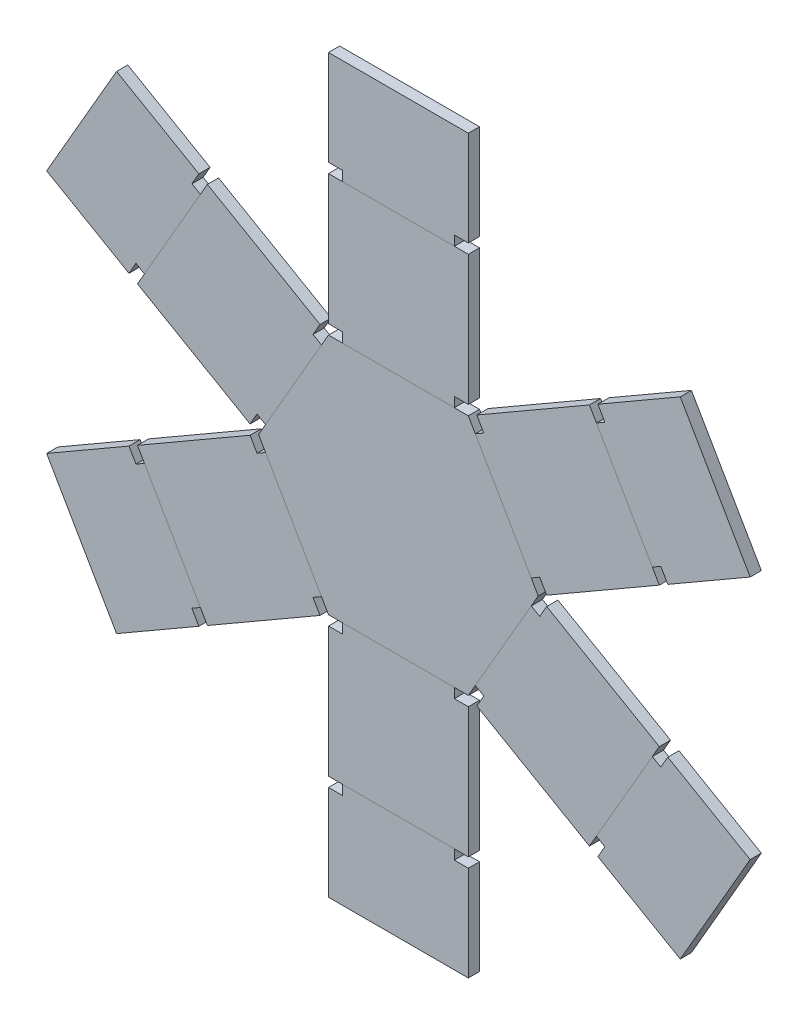
SolidWorks part; units mm, degrees
ref_plane "Front" through (0, 0, 0) normal (0, 0, 1) x (1, 0, 0)
ref_plane "Top" through (0, 0, 0) normal (0, 1, 0) x (1, 0, 0)
ref_plane "Right" through (0, 0, 0) normal (1, 0, 0) x (0, 0, -1)
sketch "Sketch1" plane through (0, 0, 0) normal (0, 0, 1) x (1, 0, 0)
  line L1 (-1, 0) -> (-0.5, -0.866)
  line L2 (-0.5, -0.866) -> (0.5, -0.866)
  line L3 (0.5, -0.866) -> (1, 0)
  line L4 (1, 0) -> (0.5, 0.866)
  line L5 (0.5, 0.866) -> (-0.5, 0.866)
  line L6 (-0.5, 0.866) -> (-1, 0)
  circle A0 centre (0, 0) radius 0.866 construction
  dimension "D1" = 2
extrude "Boss-Extrude1" add sketch "Sketch1" along normal blind 0.08
sketch "Sketch2" plane through (0, 0, 0.08) normal (0, 0, 1) x (1, 0, 0)
  line L0 (-0.95, 0.0866) -> (-0.55, 0.7794)
  line L1 (-1.0606, 0.035) -> (-1.866, 0.5)
  line L2 (-0.5606, 0.901) -> (-1.366, 1.366)
  line L3 (-1.866, 0.5) -> (-1.366, 1.366)
  line L26 (-0.95, 0.0866) -> (-1.0106, 0.1216)
  line L27 (-1.0606, 0.035) -> (-1.0106, 0.1216)
  line L30 (-0.55, 0.7794) -> (-0.6106, 0.8144)
  line L31 (-0.5606, 0.901) -> (-0.6106, 0.8144)
  line L32 (-0.5, 0.866) -> (-1, 0) construction
  line L33 (-1, 0) -> (-1.0606, 0.035) construction
  line L34 (-0.5, 0.866) -> (-0.5606, 0.901) construction
  line L35 (-0.4, 0.866) -> (0.4, 0.866)
  line L36 (0.4, 0.866) -> (0.4, 0.936)
  line L37 (0.5, 0.936) -> (0.4, 0.936)
  line L38 (0.5, 0.936) -> (0.5, 1.866)
  line L39 (-0.5, 1.866) -> (0.5, 1.866)
  line L40 (-0.5, 0.936) -> (-0.5, 1.866)
  line L41 (-0.5, 0.936) -> (-0.4, 0.936)
  line L42 (-0.4, 0.866) -> (-0.4, 0.936)
  line L43 (0.55, 0.7794) -> (0.95, 0.0866)
  line L44 (0.95, 0.0866) -> (1.0106, 0.1216)
  line L45 (1.0606, 0.035) -> (1.0106, 0.1216)
  line L46 (1.0606, 0.035) -> (1.866, 0.5)
  line L47 (1.366, 1.366) -> (1.866, 0.5)
  line L48 (0.5606, 0.901) -> (1.366, 1.366)
  line L49 (0.5606, 0.901) -> (0.6106, 0.8144)
  line L50 (0.55, 0.7794) -> (0.6106, 0.8144)
  line L51 (0.95, -0.0866) -> (0.55, -0.7794)
  line L52 (0.55, -0.7794) -> (0.6106, -0.8144)
  line L53 (0.5606, -0.901) -> (0.6106, -0.8144)
  line L54 (0.5606, -0.901) -> (1.366, -1.366)
  line L55 (1.866, -0.5) -> (1.366, -1.366)
  line L56 (1.0606, -0.035) -> (1.866, -0.5)
  line L57 (1.0606, -0.035) -> (1.0106, -0.1216)
  line L58 (0.95, -0.0866) -> (1.0106, -0.1216)
  line L59 (0.4, -0.866) -> (-0.4, -0.866)
  line L60 (-0.4, -0.866) -> (-0.4, -0.936)
  line L61 (-0.5, -0.936) -> (-0.4, -0.936)
  line L62 (-0.5, -0.936) -> (-0.5, -1.866)
  line L63 (0.5, -1.866) -> (-0.5, -1.866)
  line L64 (0.5, -0.936) -> (0.5, -1.866)
  line L65 (0.5, -0.936) -> (0.4, -0.936)
  line L66 (0.4, -0.866) -> (0.4, -0.936)
  line L67 (-0.55, -0.7794) -> (-0.95, -0.0866)
  line L68 (-0.95, -0.0866) -> (-1.0106, -0.1216)
  line L69 (-1.0606, -0.035) -> (-1.0106, -0.1216)
  line L70 (-1.0606, -0.035) -> (-1.866, -0.5)
  line L71 (-1.366, -1.366) -> (-1.866, -0.5)
  line L72 (-0.5606, -0.901) -> (-1.366, -1.366)
  line L73 (-0.5606, -0.901) -> (-0.6106, -0.8144)
  line L74 (-0.55, -0.7794) -> (-0.6106, -0.8144)
  point P29 (0, 0)
  point P59 (0, 0)
  dimension "D1" = 1
  dimension "D2" = 0.07
  dimension "D3" = 0.1
  dimension "D4" = 0.1
  dimension "D5" = 0.07
  dimension "D6" = 6
extrude "Boss-Extrude3" add sketch "Sketch2" against normal blind 0.08 separate body
sketch "Sketch3" plane through (0, 0, 0.08) normal (0, 0, 1) x (1, 0, 0)
  line L4 (-1.416, 1.2794) -> (-1.816, 0.5866)
  line L5 (-1.4266, 1.401) -> (-2.0155, 1.741)
  line L6 (-2.0155, 1.741) -> (-2.5155, 0.875)
  line L7 (-1.9266, 0.535) -> (-2.5155, 0.875)
  line L24 (-1.9266, 0.535) -> (-1.4266, 1.401) construction
  line L25 (-1.9266, 0.535) -> (-1.8766, 0.6216)
  line L26 (-1.8766, 0.6216) -> (-1.816, 0.5866)
  line L27 (-1.4266, 1.401) -> (-1.4766, 1.3144)
  line L28 (-1.4766, 1.3144) -> (-1.416, 1.2794)
  line L29 (-1.866, 0.5) -> (-1.366, 1.366) construction
  line L30 (-0.5606, 0.901) -> (-1.366, 1.366) construction
  line L31 (-1.0606, 0.035) -> (-1.866, 0.5) construction
  line L32 (0.4, 1.866) -> (-0.4, 1.866)
  line L33 (-0.4, 1.936) -> (-0.4, 1.866)
  line L34 (-0.5, 1.936) -> (-0.4, 1.936)
  line L35 (-0.5, 1.936) -> (-0.5, 2.616)
  line L36 (0.5, 2.616) -> (-0.5, 2.616)
  line L37 (0.5, 1.936) -> (0.5, 2.616)
  line L38 (0.5, 1.936) -> (0.4, 1.936)
  line L39 (0.4, 1.936) -> (0.4, 1.866)
  line L40 (1.816, 0.5866) -> (1.416, 1.2794)
  line L41 (1.4766, 1.3144) -> (1.416, 1.2794)
  line L42 (1.4266, 1.401) -> (1.4766, 1.3144)
  line L43 (1.4266, 1.401) -> (2.0155, 1.741)
  line L44 (2.5155, 0.875) -> (2.0155, 1.741)
  line L45 (1.9266, 0.535) -> (2.5155, 0.875)
  line L46 (1.9266, 0.535) -> (1.8766, 0.6216)
  line L47 (1.8766, 0.6216) -> (1.816, 0.5866)
  line L48 (1.416, -1.2794) -> (1.816, -0.5866)
  line L49 (1.8766, -0.6216) -> (1.816, -0.5866)
  line L50 (1.9266, -0.535) -> (1.8766, -0.6216)
  line L51 (1.9266, -0.535) -> (2.5155, -0.875)
  line L52 (2.0155, -1.741) -> (2.5155, -0.875)
  line L53 (1.4266, -1.401) -> (2.0155, -1.741)
  line L54 (1.4266, -1.401) -> (1.4766, -1.3144)
  line L55 (1.4766, -1.3144) -> (1.416, -1.2794)
  line L56 (-0.4, -1.866) -> (0.4, -1.866)
  line L57 (0.4, -1.936) -> (0.4, -1.866)
  line L58 (0.5, -1.936) -> (0.4, -1.936)
  line L59 (0.5, -1.936) -> (0.5, -2.616)
  line L60 (-0.5, -2.616) -> (0.5, -2.616)
  line L61 (-0.5, -1.936) -> (-0.5, -2.616)
  line L62 (-0.5, -1.936) -> (-0.4, -1.936)
  line L63 (-0.4, -1.936) -> (-0.4, -1.866)
  line L64 (-1.816, -0.5866) -> (-1.416, -1.2794)
  line L65 (-1.4766, -1.3144) -> (-1.416, -1.2794)
  line L66 (-1.4266, -1.401) -> (-1.4766, -1.3144)
  line L67 (-1.4266, -1.401) -> (-2.0155, -1.741)
  line L68 (-2.5155, -0.875) -> (-2.0155, -1.741)
  line L69 (-1.9266, -0.535) -> (-2.5155, -0.875)
  line L70 (-1.9266, -0.535) -> (-1.8766, -0.6216)
  line L71 (-1.8766, -0.6216) -> (-1.816, -0.5866)
  point P29 (0, 0)
  point P61 (0, 0)
  dimension "D1" = 0.75
  dimension "D3" = 0.07
  dimension "D4" = 0.1
  dimension "D5" = 0.1
  dimension "D2" = 6
extrude "Boss-Extrude4" add sketch "Sketch3" against normal blind 0.08 separate body
other "Save Bodies3"
